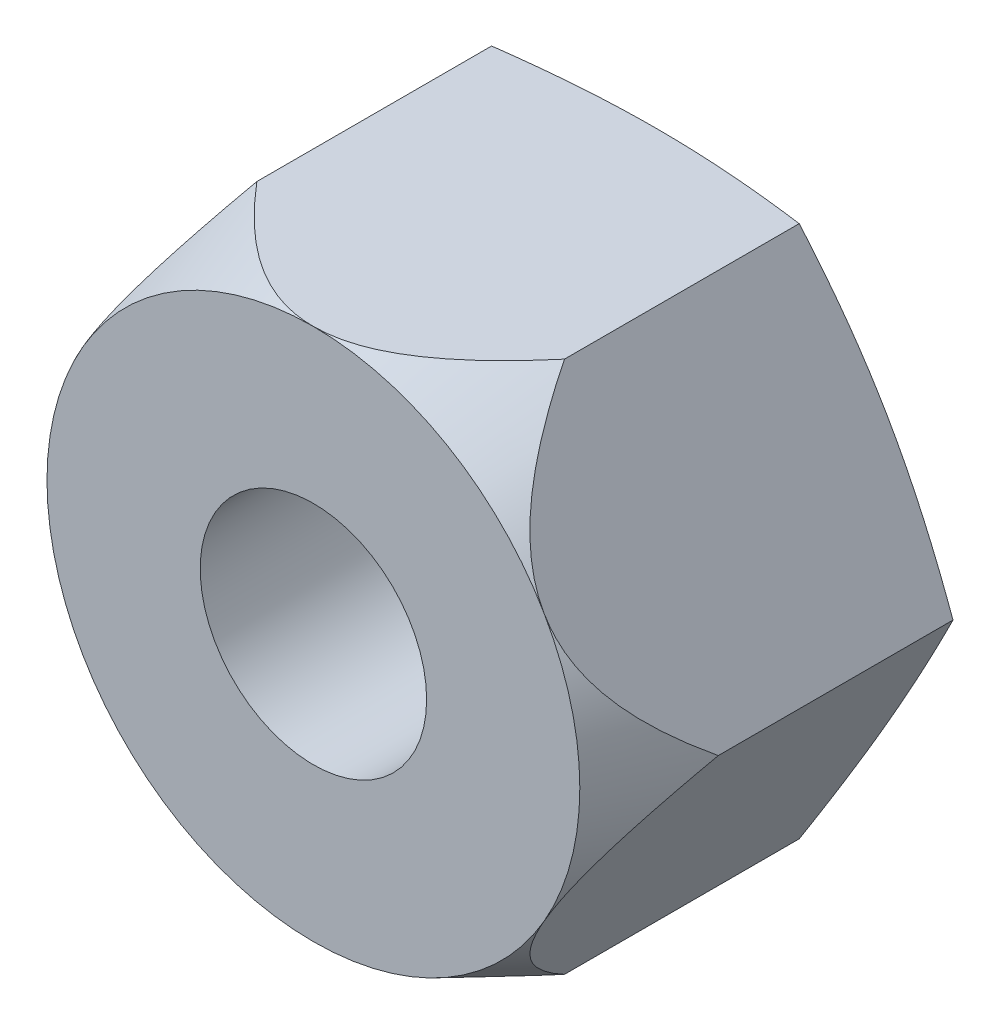
SolidWorks part; units mm, degrees
ref_plane "Front" through (0, 0, 0) normal (0, 0, 1) x (1, 0, 0)
ref_plane "Top" through (0, 0, 0) normal (0, 1, 0) x (1, 0, 0)
ref_plane "Right" through (0, 0, 0) normal (1, 0, 0) x (0, 0, -1)
sketch "Sketch1" plane through (0, 0, 0) normal (0, 0, 1) x (1, 0, 0)
  line L1 (2.3094, -4) -> (4.6188, 0)
  line L2 (4.6188, 0) -> (2.3094, 4)
  line L3 (2.3094, 4) -> (-2.3094, 4)
  line L4 (-2.3094, 4) -> (-4.6188, 0)
  line L5 (-4.6188, 0) -> (-2.3094, -4)
  line L6 (-2.3094, -4) -> (2.3094, -4)
  circle A0 centre (0, 0) radius 4 construction
  dimension "s" = 8
extrude "BaseNut" add sketch "Sketch1" against normal blind 5.3
sketch "Sketch2" plane through (0.4812, 0, -5.1) normal (0, -1, 0) x (0, 0, -1)
  line L0 (-0.1158, 4.1376) -> (0.2, 4.1376)
  line L2 (0.2, 4.1376) -> (0.2, 2.9588)
  line L3 (-5.1, 1.8282) -> (-5.1, 4.1376) construction
  line L4 (0.2, 2.9588) -> (-0.1158, 4.1376)
  line L5 (-5.1, 4.1376) -> (-3.64, 4.1376)
  line L6 (-5.1, 4.1376) -> (-5.1, 3.5188)
  line L7 (0.2, 1.8282) -> (0.2, 4.1376) construction
  line L8 (-5.1, 3.5188) -> (-3.64, 4.1376)
  line L9 (-0.6371, -0.4812) -> (-5.5811, -0.4812) construction
  line L10 (0.2, 4.1376) -> (-5.1, 4.1376) construction
  dimension "e" = 8
  dimension "D" = 6.88
  dimension "D4" = 15
  dimension "m1" = 3.84
revolve "Double-Chamfer" cut sketch "Sketch2" angle 360 about L9
sketch "Sketch3" plane through (0, 0, 0) normal (0, 0, 1) x (1, 0, 0)
  circle A0 centre (0, 0) radius 1.7
  dimension "D1" = 3.4
extrude "Hole" cut sketch "Sketch3" against normal through all
cosmetic thread "ThreadCosmetic1" [suppressed] parameters "D2"=5
chamfer "EndChamfer" distance 0.4857 angle 45 1 edges at (1.7, 0, -5.3)
sketch "Sketch4" plane through (0, 0, 0) normal (0, 1, 0) x (1, 0, 0)
  line L0 (0, 6.8088) -> (0, -0.7438) construction
  line L1 (0.9, 5.2143) -> (1.7, 5.2143)
  line L2 (1.7, 5.2143) -> (2.3928, 4.8143)
  line L3 (2.3928, 4.8143) -> (1.7, 4.4143)
  line L4 (1.7, 4.4143) -> (0.9, 4.4143)
  line L5 (0.9, 4.4143) -> (0.9, 5.2143)
  line L6 (-1.7, 4.8143) -> (1.7, 4.8143) construction
  dimension "D1" = 3.4
  dimension "D2" = 0.8
revolve "Cut-Revolve10" [suppressed] cut sketch "Sketch4" angle 360 about L0
pattern_linear "LPattern10" [suppressed] count 5 spacing 0.96 along (0, 0, 1)
equation "\"e@Sketch2\" = \"s@Sketch1\""
equation "\"D1@Sketch4\" = \"D1@Sketch3\""
equation "\"D2@Sketch4\" = (  \"D2@ThreadCosmetic1\" - \"D1@Sketch3\" )  / 2"
equation "\"D3@LPattern10\" = \"D2@Sketch4\" * 1.2"
equation "\"D1@LPattern10\" = (  \"h@BaseNut\"  - \"D1@EndChamfer\" ) / \"D3@LPattern10\" "
equation "\"D1@EndChamfer\" = \"D1@Sketch3\" / 7"
